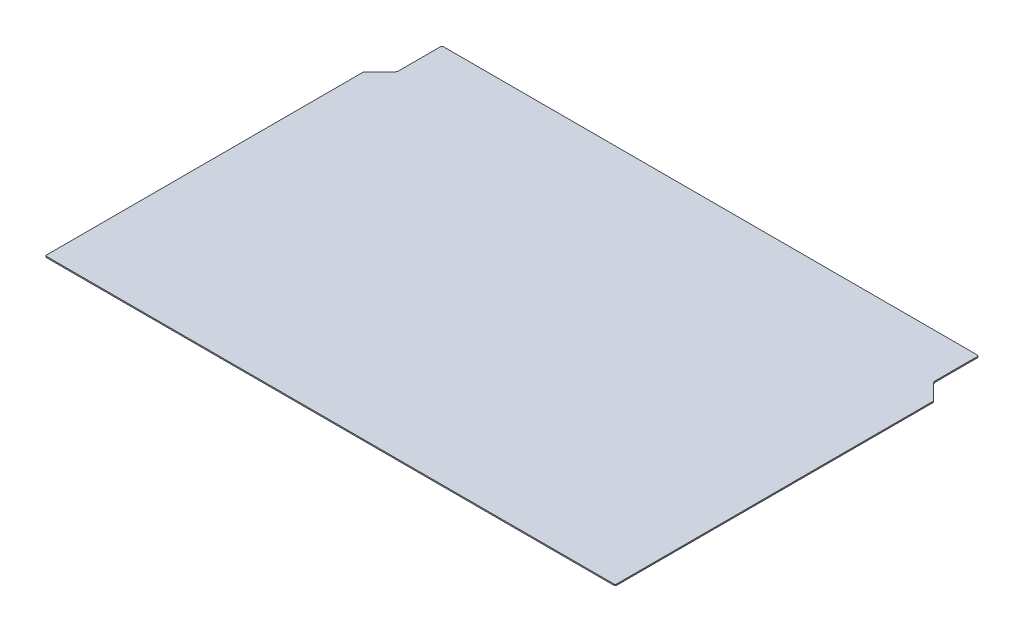
SolidWorks part; units mm, degrees
material "PE High Density"
ref_plane "Front Plane" through (0, 0, 0) normal (0, 0, 1) x (1, 0, 0)
ref_plane "Top Plane" through (0, 0, 0) normal (0, 1, 0) x (1, 0, 0)
ref_plane "Right Plane" through (0, 0, 0) normal (1, 0, 0) x (0, 0, -1)
sketch "Sketch1" plane through (0, 0, 0) normal (0, 1, 0) x (1, 0, 0)
  line L0 (-717.55, 504.825) -> (-717.55, 392.6105)
  line L1 (-758.825, -508) -> (758.825, -508)
  line L2 (-762, -504.825) -> (-762, 341.5849)
  line L3 (-714.375, 508) -> (714.375, 508)
  line L4 (762, -504.825) -> (762, 341.5849)
  line L5 (-762, -508) -> (762, 508) construction
  line L6 (-762, 508) -> (762, -508) construction
  line L8 (717.55, 504.825) -> (717.55, 392.6105)
  line L10 (-761.0701, 343.8299) -> (-721.2697, 383.6303)
  line L11 (761.0701, 343.8299) -> (721.2697, 383.6303)
  arc A2 (717.55, 392.6105) -> (721.2697, 383.6303) centre (730.25, 392.6105) ccw
  arc A3 (-721.2697, 383.6303) -> (-717.55, 392.6105) centre (-730.25, 392.6105) ccw
  arc A4 (761.0701, 343.8299) -> (762, 341.5849) centre (758.825, 341.5849) cw
  arc A5 (717.55, 504.825) -> (714.375, 508) centre (714.375, 504.825) ccw
  arc A6 (758.825, -508) -> (762, -504.825) centre (758.825, -504.825) ccw
  arc A7 (-758.825, -508) -> (-762, -504.825) centre (-758.825, -504.825) cw
  arc A8 (-761.0701, 343.8299) -> (-762, 341.5849) centre (-758.825, 341.5849) ccw
  arc A9 (-717.55, 504.825) -> (-714.375, 508) centre (-714.375, 504.825) cw
  point P0 (0, 0)
  point P18 (762, 342.9)
  point P21 (717.55, 508)
  point P30 (-762, 342.9)
  point P33 (-717.55, 508)
  dimension "D5" = 44.45
  dimension "D6" = 12.7
  dimension "D7" = 3.175
  dimension "D1" = 1524
  dimension "D2" = 1016
  dimension "D3" = 165.1
  dimension "D4" = 135
extrude "Boss-Extrude1" add sketch "Sketch1" along normal blind 3.175
sketch "Sketch2" plane through (0, 3.175, 0) normal (0, 1, 0) x (1, 0, 0)
  line L0 (-565.15, 9.525) -> (565.15, 9.525) construction
  line L1 (565.15, -269.875) -> (-565.15, -269.875) construction
  line L2 (565.15, -269.875) -> (565.15, 422.275) construction
  line L3 (565.15, 422.275) -> (-565.15, 422.275) construction
  line L4 (-565.15, -269.875) -> (-565.15, 422.275) construction
  line L5 (565.15, -269.875) -> (-565.15, 422.275) construction
  line L6 (565.15, 422.275) -> (-565.15, -269.875) construction
  line L7 (-447.675, -107.95) -> (-682.625, -107.95) construction
  line L8 (-447.675, -107.95) -> (-447.675, 127) construction
  line L9 (-447.675, 127) -> (-682.625, 127) construction
  line L10 (-682.625, -107.95) -> (-682.625, 127) construction
  line L11 (-447.675, -107.95) -> (-682.625, 127) construction
  line L12 (-447.675, 127) -> (-682.625, -107.95) construction
  line L13 (682.625, -107.95) -> (447.675, -107.95) construction
  line L14 (682.625, -107.95) -> (682.625, 127) construction
  line L15 (682.625, 127) -> (447.675, 127) construction
  line L16 (447.675, -107.95) -> (447.675, 127) construction
  line L17 (682.625, -107.95) -> (447.675, 127) construction
  line L18 (682.625, 127) -> (447.675, -107.95) construction
  line L20 (-117.475, -107.95) -> (117.475, -107.95) construction
  line L21 (-117.475, -107.95) -> (-117.475, 127) construction
  line L22 (-117.475, 127) -> (117.475, 127) construction
  line L23 (117.475, -107.95) -> (117.475, 127) construction
  line L24 (-117.475, -107.95) -> (117.475, 127) construction
  line L25 (-117.475, 127) -> (117.475, -107.95) construction
  point P0 (0, 0)
  point P5 (0, 9.525)
  point P6 (-565.15, 9.525)
  point P8 (0, 76.2)
  point P13 (565.15, 9.525)
  dimension "D1" = 1130.3
  dimension "D2" = 692.15
  dimension "D3" = 76.2
  dimension "D4" = 234.95
  dimension "D5" = 127
hole_wizard "17/64 (0.26563) Diameter Hole1" [suppressed] positions "Sketch3" profile "Sketch4" hole size "17/64" standard "ANSI Inch"
sketch "Sketch3" plane through (0, 3.175, 0) normal (0, 1, 0) x (1, 0, 0)
  point P0 (-565.15, 422.275)
  point P3 (565.15, 422.275)
  point P6 (565.15, -269.875)
  point P9 (-565.15, -269.875)
  point P47 (-682.625, 127)
  point P50 (-447.675, 127)
  point P53 (-682.625, -107.95)
  point P56 (-447.675, -107.95)
  point P59 (-117.475, 127)
  point P62 (117.475, 127)
  point P65 (-117.475, -107.95)
  point P68 (117.475, -107.95)
  point P71 (447.675, 127)
  point P74 (682.625, 127)
  point P77 (447.675, -107.95)
  point P80 (682.625, -107.95)
sketch "Sketch4" plane through (-565.15, 3.175, -422.275) normal (1, 0, 0) x (0, 0, 1)
  line L0 (0, 0) -> (0, 3.175)
  line L1 (0, 3.175) -> (3.3735, 3.175)
  line L2 (3.3735, 3.175) -> (3.3735, 0)
  line L5 (3.3735, 0) -> (0, 0)
  line L11 (0, -6.35) -> (0, 107.95) construction
  dimension "Thru Hole Dia." = 6.747
  dimension "Thru Hole Depth" = 3.175
sketch "Sketch5" plane through (0, 3.175, 0) normal (0, 1, 0) x (1, 0, 0)
  line L0 (-758.825, -508) -> (758.825, -508) construction
  line L1 (-127, -508) -> (127, -508)
  line L2 (-127, -508) -> (-127, -469.9)
  line L3 (-127, -469.9) -> (127, -469.9)
  line L4 (127, -508) -> (127, -469.9)
  line L5 (-762, 341.5849) -> (-762, -504.825) construction
  dimension "D1" = 254
  dimension "D2" = 38.1
  dimension "D3" = 635
extrude "Cut-Extrude1" [suppressed] cut sketch "Sketch5" against normal through all
fillet "Fillet1" [suppressed] radius 3.175
